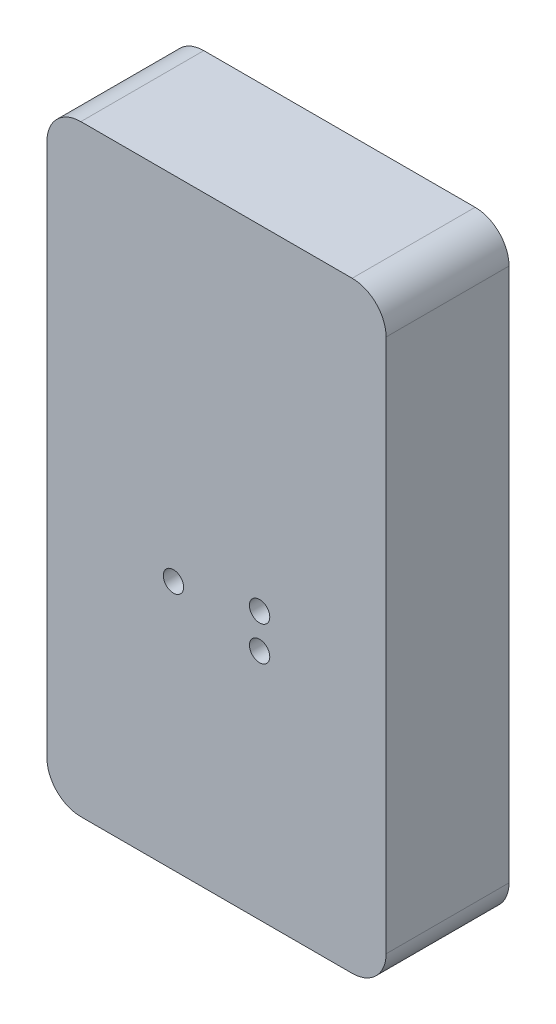
SolidWorks part; units mm, degrees
ref_plane "Front Plane" through (0, 0, 0) normal (0, 0, 1) x (1, 0, 0)
ref_plane "Top Plane" through (0, 0, 0) normal (0, 1, 0) x (1, 0, 0)
ref_plane "Right Plane" through (0, 0, 0) normal (1, 0, 0) x (0, 0, -1)
sketch "Sketch1" plane through (0, 0, 0) normal (0, 0, 1) x (1, 0, 0)
  line L1 (-10, -17.75) -> (10, -17.75)
  line L2 (-10, -17.75) -> (-10, 17.75)
  line L3 (-10, 17.75) -> (10, 17.75)
  line L4 (10, -17.75) -> (10, 17.75)
  line L5 (-10, -17.75) -> (10, 17.75) construction
  line L6 (-10, 17.75) -> (10, -17.75) construction
  point P0 (0, 0)
extrude "Boss-Extrude1" add sketch "Sketch1" along normal blind 7.25
sketch "Sketch2" plane through (0, 0, 0) normal (0, 0, 1) x (1, 0, 0)
  line L0 (-3.625, 11.125) -> (-3.625, 16.125)
  line L1 (-3.625, -16.125) -> (3.625, -16.125)
  line L2 (-3.625, -16.125) -> (-3.625, -11.125)
  line L3 (-3.625, 16.125) -> (3.625, 16.125)
  line L4 (3.625, -16.125) -> (3.625, -11.125)
  line L5 (-3.625, -16.125) -> (3.625, 16.125) construction
  line L6 (-3.625, 16.125) -> (3.625, -16.125) construction
  line L7 (-8.375, -11.125) -> (-3.625, -11.125)
  line L8 (-8.375, -11.125) -> (-8.375, 11.125)
  line L9 (-8.375, 11.125) -> (-3.625, 11.125)
  line L10 (8.375, -11.125) -> (8.375, 11.125)
  line L11 (-8.375, -11.125) -> (8.375, 11.125) construction
  line L12 (-8.375, 11.125) -> (8.375, -11.125) construction
  line L13 (3.625, 11.125) -> (8.375, 11.125)
  line L14 (3.625, 11.125) -> (3.625, 16.125)
  line L16 (3.625, -11.125) -> (8.375, -11.125)
  point P0 (0, 0)
  point P6 (0, 0)
extrude "Cut-Extrude1" cut sketch "Sketch2" along normal blind 5.75
sketch "Sketch3" plane through (0, 0, 0) normal (0, 0, 1) x (1, 0, 0)
  circle A0 centre (-2.54, -3) radius 0.6
  circle A1 centre (2.54, -1.984) radius 0.6
  circle A2 centre (2.54, -4.016) radius 0.6
  point P9 (-1.538, -1.4765)
  dimension "D1" = 3
  dimension "D2" = 2.54
  dimension "D3" = 1.984
  dimension "D4" = 2.54
  dimension "D5" = 2.54
  dimension "D6" = 4.016
extrude "Cut-Extrude2" cut sketch "Sketch3" along normal blind 7.25
fillet "Fillet1" radius 2 4 edges at (-10, 17.75, 3.625) (10, 17.75, 3.625) (10, -17.75, 3.625) (-10, -17.75, 3.625)
sketch "Sketch4" plane through (0, 0, 0) normal (0, 0, 1) x (1, 0, 0)
  line L0 (-3.625, 12.5) -> (-10, 12.5) construction
  line L2 (-10, 15.75) -> (-10, -15.75) construction
  line L3 (3.625, -13) -> (9, -13) construction
  text T0 "<b>+</b>"
  text T1 "<b>-</b>" font "Century Gothic" height 3.5
extrude "Cut-Extrude3" cut sketch "Sketch4" along normal blind 1
chamfer "Chamfer1" distance 0.5 angle 45 12 edges at (-6, -11.125, 0) (-3.625, -13.625, 0) (0, -16.125, 0) (3.625, -13.625, 0) (6, -11.125, 0) (-8.375, 0, 0) (-6, 11.125, 0) (-3.625, 13.625, 0) (0, 16.125, 0) (3.625, 13.625, 0) (6, 11.125, 0) (8.375, 0, 0)
